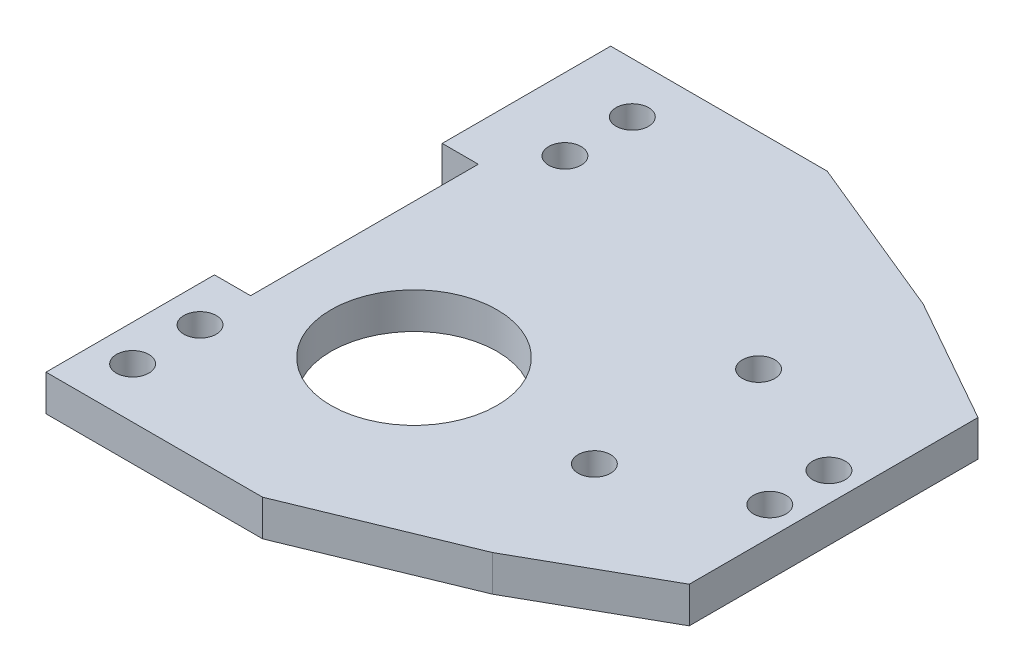
SolidWorks part; units mm, degrees
ref_plane "Front Plane" through (0, 0, 0) normal (0, 0, 1) x (1, 0, 0)
ref_plane "Top Plane" through (0, 0, 0) normal (0, 1, 0) x (1, 0, 0)
ref_plane "Right Plane" through (0, 0, 0) normal (1, 0, 0) x (0, 0, -1)
ref_plane "Plane1" through (0, -5, 0) normal (0, -1, 0) x (1, 0, 0)
sketch "Sketch1" plane through (0, -5, 0) normal (0, -1, 0) x (1, 0, 0)
  line L0 (-35.7506, 15.7744) -> (-35.7506, -15.7744)
  line L1 (-35.7506, -15.7744) -> (-40.7506, -15.7744)
  line L2 (-40.7506, -15.7744) -> (-40.7506, -39.1126)
  line L3 (-40.7506, -39.1126) -> (-10.7506, -39.1126)
  line L4 (-10.7506, -39.1126) -> (11.8282, -29.8236)
  line L5 (11.8282, -29.8236) -> (29.2494, -20)
  line L6 (29.2494, -20) -> (29.2494, 20)
  line L7 (29.2494, 20) -> (11.8282, 29.8236)
  line L8 (11.8282, 29.8236) -> (-10.7506, 39.1126)
  line L9 (-10.7506, 39.1126) -> (-40.7506, 39.1126)
  line L10 (-40.7506, 39.1126) -> (-40.7506, 15.7744)
  line L11 (-40.7506, 15.7744) -> (-35.7506, 15.7744)
  line L12 (-49.9871, -32.1126) -> (-17.3747, -32.1126) construction
  line L13 (-50.834, -22.7744) -> (-17.3747, -22.7744) construction
  line L14 (-46.5346, 12.236) -> (-2.7037, 12.236) construction
  line L15 (-50.834, 22.7744) -> (-25.8706, 22.7744) construction
  line L16 (-50.834, 32.1126) -> (-25.8706, 32.1126) construction
  line L17 (-17.0034, -4.7862) -> (-17.0034, 28.5435) construction
  circle A0 centre (-30.7506, -22.7744) radius 2.25
  circle A1 centre (25.2728, -3.3297) radius 2.25
  circle A2 centre (8.2466, -10.6061) radius 2.25
  circle A3 centre (25.2728, 4.8676) radius 2.25
  circle A4 centre (-30.7506, -32.1126) radius 2.25
  circle A6 centre (-17.0034, 11.8786) radius 11.5
  circle A9 centre (8.2466, 12.1439) radius 2.25
  circle A10 centre (-35.7506, 22.7744) radius 2.25
  circle A11 centre (-35.7506, 32.1126) radius 2.25
  point P12 (0, 0)
  dimension "D2" = 4.5
  dimension "D3" = 4.5
  dimension "D4" = 4.5
  dimension "D5" = 4.5
  dimension "D10" = 4.5
  dimension "D11" = 4.5
  dimension "D14" = 4.5
  dimension "D15" = 4.5
  dimension "D16" = 23
  dimension "D1" = 70
  dimension "D6" = 10
  dimension "D7" = 10
  dimension "D8" = 7
  dimension "D9" = 7
  dimension "D12" = 7
  dimension "D13" = 7
extrude "Boss-Extrude1" add sketch "Sketch1" against normal blind 5
